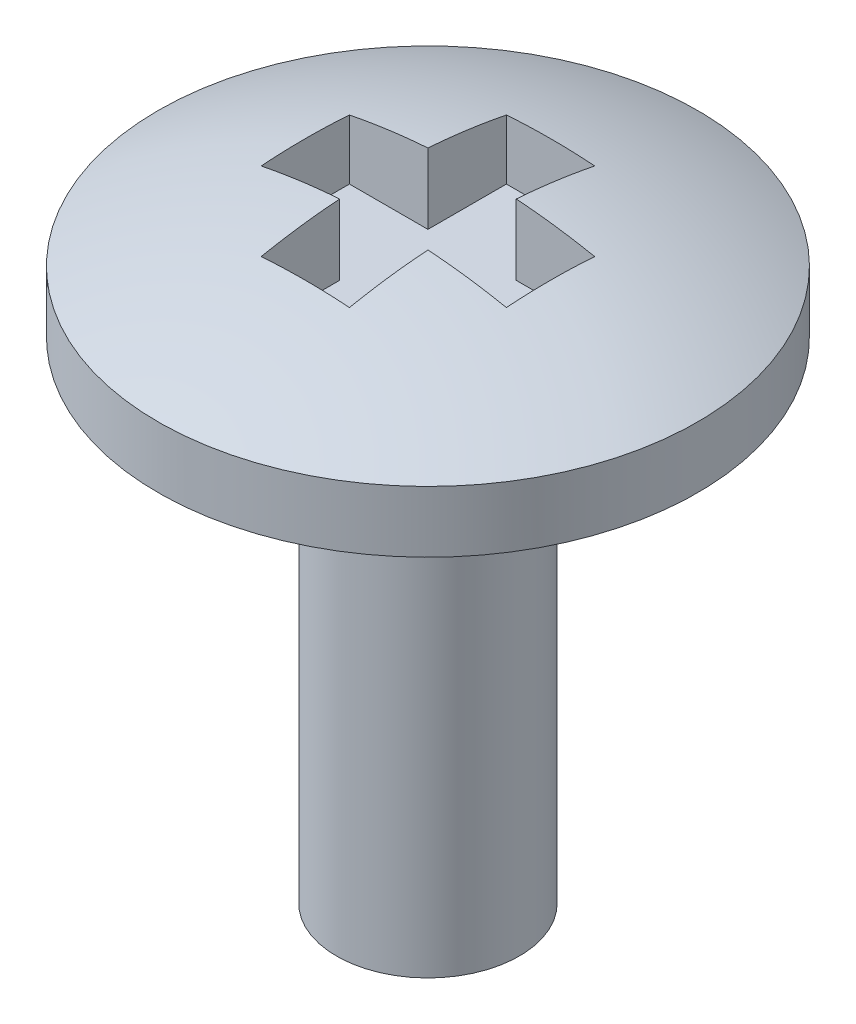
SolidWorks part; units mm, degrees
material "ASTM A36 Steel"
ref_plane "Front Plane" through (0, 0, 0) normal (0, 0, 1) x (1, 0, 0)
ref_plane "Top Plane" through (0, 0, 0) normal (0, 1, 0) x (1, 0, 0)
ref_plane "Right Plane" through (0, 0, 0) normal (1, 0, 0) x (0, 0, -1)
sketch "Sketch1" plane through (0, 0, 0) normal (0, 0, 1) x (1, 0, 0)
  line L0 (0, 0) -> (0, -6.35)
  line L1 (0, -6.35) -> (0.9466, -6.35)
  line L2 (0.9466, -6.35) -> (0.9466, -1.27)
  line L3 (0.9466, -1.27) -> (2.794, -1.27)
  line L4 (2.794, -1.27) -> (2.794, -0.635)
  line L5 (0, 0) -> (-0.8754, 0) construction
  arc A0 (0, 0) -> (2.794, -0.635) centre (0, -6.4643) cw
  dimension "D1" = 6.35
  dimension "D2" = 2.794
  dimension "D3" = 0.635
  dimension "D4" = 1.27
revolve "Revolve1" add sketch "Sketch1" angle 360 about L0
ref_plane "Plane1" through (0, -0.762, 0) normal (0, -1, 0) x (1, 0, 0)
sketch "Sketch2" plane through (0, -0.762, 0) normal (0, -1, 0) x (1, 0, 0)
  line L0 (0, -1.27) -> (0, 1.27) construction
  line L1 (-1.27, 0) -> (1.27, 0) construction
  line L2 (0.4572, -1.27) -> (-0.4572, -1.27)
  line L3 (-0.4572, 1.27) -> (0.4572, 1.27)
  line L4 (-1.27, -0.4572) -> (-1.27, 0.4572)
  line L5 (1.27, -0.4572) -> (1.27, 0.4572)
  line L6 (-1.27, -0.4572) -> (-0.4572, -0.4572)
  line L7 (-1.27, 0.4572) -> (-0.4572, 0.4572)
  line L8 (-0.4572, -1.27) -> (-0.4572, -0.4572)
  line L9 (0.4572, -1.27) -> (0.4572, -0.4572)
  line L10 (0.4572, 0.4572) -> (0.4572, 1.27)
  line L11 (0.4572, -0.4572) -> (1.27, -0.4572)
  line L12 (-0.4572, 0.4572) -> (-0.4572, 1.27)
  line L13 (0.4572, 0.4572) -> (1.27, 0.4572)
  dimension "D1" = 2.54
  dimension "D2" = 0.9144
extrude "Extrude1" cut sketch "Sketch2" against normal blind 2.54
